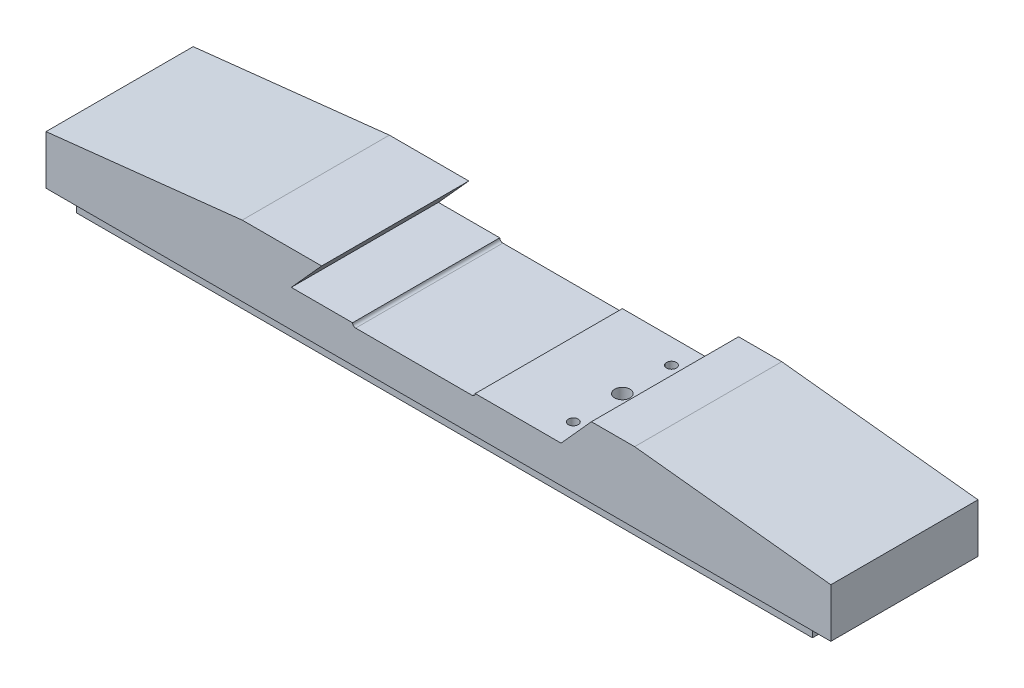
SolidWorks part; units mm, degrees
material "Gray Cast Iron"
ref_plane "Front Plane" through (0, 0, 0) normal (0, 0, 1) x (1, 0, 0)
ref_plane "Top Plane" through (0, 0, 0) normal (0, 1, 0) x (1, 0, 0)
ref_plane "Right Plane" through (0, 0, 0) normal (1, 0, 0) x (0, 0, -1)
ref_plane "Plane4" through (0, 0, -76.2) normal (0, 0, -1) x (-1, 0, 0)
sketch "Sketch1" plane through (0, 0, -76.2) normal (0, 0, -1) x (-1, 0, 0)
  line L0 (0, 0) -> (0, 25.4)
  line L1 (0, 25.4) -> (-101.6, 36.5125)
  line L2 (-101.6, 36.5125) -> (-142.7233, 36.5125)
  line L3 (-142.7233, 36.5125) -> (-127, 19.05)
  line L4 (-127, 19.05) -> (-158.75, 19.05)
  line L5 (-160.3375, 17.4625) -> (-220.6625, 17.4625)
  line L6 (-222.25, 19.05) -> (-266.7, 19.05)
  line L7 (-266.7, 19.05) -> (-284.4294, 38.7405)
  line L8 (-284.4294, 38.7405) -> (-406.4, 25.4)
  line L9 (-406.4, 25.4) -> (-406.4, 0)
  line L10 (-406.4, 0) -> (0, 0)
  arc A0 (-158.75, 19.05) -> (-160.3375, 17.4625) centre (-160.3375, 19.05) cw
  arc A1 (-220.6625, 17.4625) -> (-222.25, 19.05) centre (-220.6625, 19.05) cw
extrude "Boss-Extrude1" add sketch "Sketch1" against normal blind 76.2
ref_plane "Plane5" through (0, 0, 0) normal (-1, 0, 0) x (0, -1, 0)
sketch "Sketch2" plane through (0, 0, 0) normal (-1, 0, 0) x (0, -1, 0)
  line L0 (0, -25.4) -> (0, -50.8)
  line L1 (0, -50.8) -> (9.525, -50.8)
  line L2 (9.525, -50.8) -> (9.525, -60.325)
  line L3 (9.525, -60.325) -> (19.05, -60.325)
  line L4 (19.05, -60.325) -> (19.05, -15.875)
  line L5 (19.05, -15.875) -> (9.525, -15.875)
  line L6 (9.525, -15.875) -> (9.525, -25.4)
  line L7 (9.525, -25.4) -> (0, -25.4)
extrude "Boss-Extrude2" add sketch "Sketch2" against normal blind 381
hole_wizard "1/4-20 Tapped Hole3" positions "Sketch4" profile "Sketch3" tap size "1/4-20" standard "ANSI Inch"
sketch "Sketch4" plane through (0, 0, 0) normal (0, -1, 0) x (-1, 0, 0)
  point P0 (-393.7, 65.0875)
  point P1 (-393.7, 11.1125)
sketch "Sketch3" plane through (393.7, 0, -65.0875) normal (1, 0, 0) x (0, 0, -1)
  line L0 (0, 0) -> (0, 20.5838)
  line L1 (0, 20.5838) -> (2.5527, 19.05)
  line L2 (2.5527, 19.05) -> (2.5527, 0)
  line L5 (2.5527, 0) -> (0, 0)
  line L10 (0, 20.5838) -> (-2.5527, 19.05) construction
  line L11 (0, -6.35) -> (0, 107.95) construction
  dimension "Tap Drill Dia." = 5.1054
  dimension "Tap Drill Depth" = 19.05
  dimension "Drill Angle" = 118
cosmetic thread "Hole Thread6" parameters "D1"=12.7, "D2"=6.35
cosmetic thread "Hole Thread7" parameters "D1"=12.7, "D2"=6.35
hole_wizard "1/4-20 Tapped Hole2" positions "Sketch6" profile "Sketch5" tap size "1/4-20" standard "ANSI Inch"
sketch "Sketch6" plane through (0, 0, -76.2) normal (0, 0, -1) x (-1, 0, 0)
  point P0 (-139.7, 9.525)
  point P1 (-241.3, 9.525)
sketch "Sketch5" plane through (139.7, 9.525, -76.2) normal (1, 0, 0) x (0, 1, 0)
  line L0 (0, 0) -> (0, 20.5838)
  line L1 (0, 20.5838) -> (2.5527, 19.05)
  line L2 (2.5527, 19.05) -> (2.5527, 0)
  line L5 (2.5527, 0) -> (0, 0)
  line L10 (0, 20.5838) -> (-2.5527, 19.05) construction
  line L11 (0, -6.35) -> (0, 107.95) construction
  dimension "Tap Drill Dia." = 5.1054
  dimension "Tap Drill Depth" = 19.05
  dimension "Drill Angle" = 118
cosmetic thread "Hole Thread4" parameters "D1"=12.7, "D2"=6.35
cosmetic thread "Hole Thread5" parameters "D1"=12.7, "D2"=6.35
hole_wizard "3/8-16 Tapped Hole1" positions "Sketch8" profile "Sketch7" tap size "3/8-16" standard "ANSI Inch"
sketch "Sketch8" plane through (0, 19.05, 0) normal (0, 1, 0) x (1, 0, 0)
  point P0 (260.35, 38.1)
sketch "Sketch7" plane through (260.35, 19.05, -38.1) normal (1, 0, 0) x (0, 0, 1)
  line L0 (0, 0) -> (0, 29.3087)
  line L1 (0, 29.3087) -> (3.9687, 26.924)
  line L2 (3.9687, 26.924) -> (3.9687, 0)
  line L5 (3.9687, 0) -> (0, 0)
  line L10 (0, 29.3087) -> (-3.9688, 26.924) construction
  line L11 (0, -6.35) -> (0, 107.95) construction
  dimension "Tap Drill Dia." = 7.9375
  dimension "Tap Drill Depth" = 26.924
  dimension "Drill Angle" = 118
cosmetic thread "Hole Thread3" parameters "D1"=19.05, "D2"=9.525
hole_wizard "1/4-20 Tapped Hole1" positions "Sketch10" profile "Sketch9" tap size "1/4-20" standard "ANSI Inch"
sketch "Sketch10" plane through (0, 19.05, 0) normal (0, 1, 0) x (1, 0, 0)
  point P0 (260.35, 12.7)
  point P1 (260.35, 63.5)
sketch "Sketch9" plane through (260.35, 19.05, -12.7) normal (1, 0, 0) x (0, 0, 1)
  line L0 (0, 0) -> (0, 18.9963)
  line L1 (0, 18.9963) -> (2.5527, 17.4625)
  line L2 (2.5527, 17.4625) -> (2.5527, 0)
  line L5 (2.5527, 0) -> (0, 0)
  line L10 (0, 18.9963) -> (-2.5527, 17.4625) construction
  line L11 (0, -6.35) -> (0, 107.95) construction
  dimension "Tap Drill Dia." = 5.1054
  dimension "Tap Drill Depth" = 17.4625
  dimension "Drill Angle" = 118
cosmetic thread "Hole Thread1" parameters "D1"=12.7, "D2"=6.35
cosmetic thread "Hole Thread2" parameters "D1"=12.7, "D2"=6.35
chamfer "Chamfer1" distance 20.492 angle 6.242 1 edges at (284.4294, 38.7405, -38.1)
